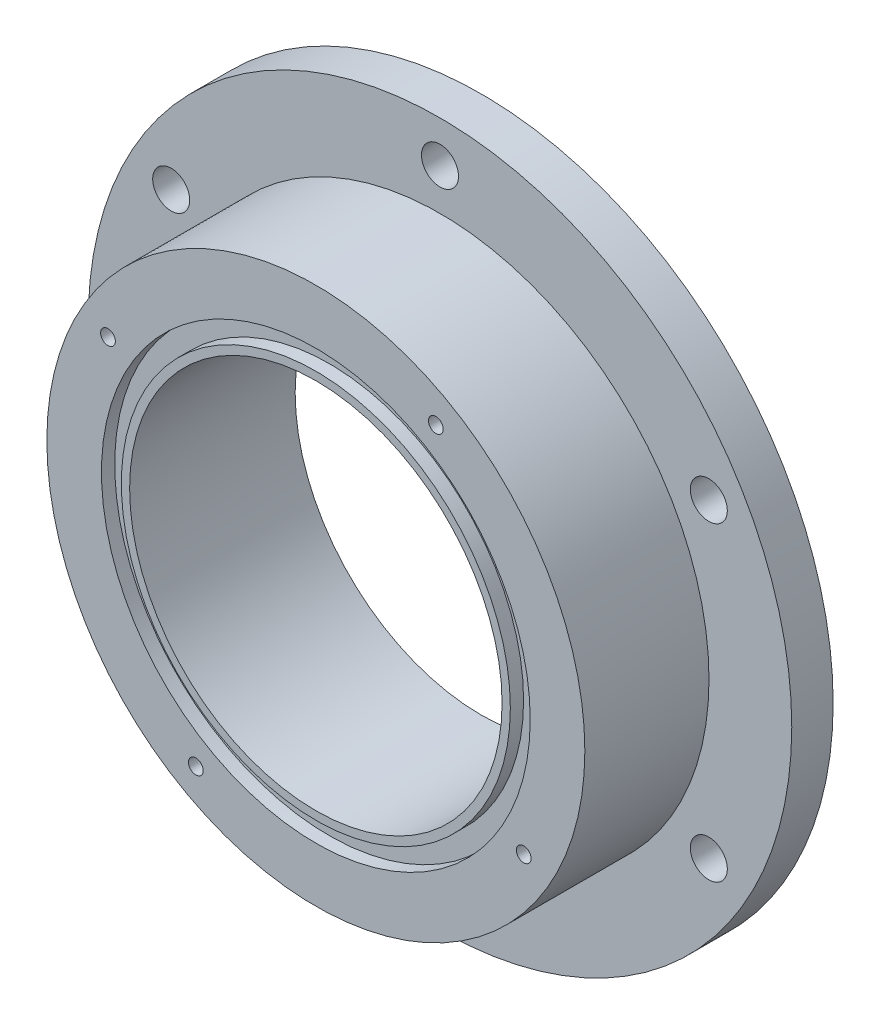
SolidWorks part; units mm, degrees
ref_plane "Front Plane" through (0, 0, 0) normal (0, 0, 1) x (1, 0, 0)
ref_plane "Top Plane" through (0, 0, 0) normal (0, 1, 0) x (1, 0, 0)
ref_plane "Right Plane" through (0, 0, 0) normal (1, 0, 0) x (0, 0, -1)
sketch "Sketch1" plane through (0, 0, 0) normal (0, 0, 1) x (1, 0, 0)
  circle A0 centre (0, 0) radius 53.975
  dimension "D1" = 107.95
extrude "Boss-Extrude1" add sketch "Sketch1" along normal blind 25.4
sketch "Sketch2" plane through (0, 0, 25.4) normal (0, 0, 1) x (1, 0, 0)
  circle A0 centre (0, 0) radius 41.275
  dimension "D1" = 82.55
extrude "Cut-Extrude1" cut sketch "Sketch2" along direction (0, 0, 1) on the side against the normal offset from surface (19.05 mm away) 6.35 flip side to cut
sketch "Sketch3" plane through (0, 0, 25.4) normal (0, 0, 1) x (1, 0, 0)
  circle A0 centre (0, 0) radius 28.575
  dimension "D1" = 57.15
extrude "Cut-Extrude2" cut sketch "Sketch3" against normal through all
sketch "Sketch6" plane through (0, 0, 25.4) normal (0, 0, 1) x (1, 0, 0)
  circle A0 centre (0, 0) radius 29.845
  circle A1 centre (0, 0) radius 32.893
  dimension "D1" = 59.69
  dimension "D2" = 3.048
extrude "Cut-Extrude3" cut sketch "Sketch6" against normal blind 2.032
hole_wizard "#4-40 Tapped Hole1" positions "Sketch7" profile "Sketch8" tap size "#4-40" standard "ANSI Inch"
sketch "Sketch7" plane through (0, 0, 25.4) normal (0, 0, 1) x (1, 0, 0)
  line L0 (0, 0) -> (0, 23.9657) construction
  line L2 (18.064, 9.5304) -> (18.2235, 9.5304) construction
  line L4 (0, 0) -> (38.7215, 67.0676) construction
  line L6 (67.9094, 49.8055) -> (68.0689, 49.8055) construction
  point P0 (18.415, 31.8957)
  dimension "D1" = 30
  dimension "D2" = 36.83
sketch "Sketch8" plane through (18.415, 31.8957, 25.4) normal (1, 0, 0) x (0, -1, 0)
  line L0 (0, 0) -> (0, 10.9662)
  line L1 (0, 10.9662) -> (1.1303, 10.287)
  line L2 (1.1303, 10.287) -> (1.1303, 0)
  line L5 (1.1303, 0) -> (0, 0)
  line L10 (0, 10.9662) -> (-1.1303, 10.287) construction
  line L11 (0, -6.35) -> (0, 107.95) construction
  dimension "Tap Drill Dia." = 2.2606
  dimension "Tap Drill Depth" = 10.287
  dimension "Drill Angle" = 118
pattern_circular "CirPattern2" count 4 over 360 about axis through (0, 0, 0) along (0, 0, 1) of "#4-40 Tapped Hole1"
sketch "Sketch9" plane through (0, 0, 0) normal (0, 0, -1) x (-1, 0, 0)
  circle A0 centre (0, 47.625) radius 2.8406
  dimension "D1" = 47.625
extrude "Cut-Extrude4" cut sketch "Sketch9" against normal through all
pattern_circular "CirPattern4" count 6 over 360 about axis through (0, 0, 0) along (0, 0, 1) of "Cut-Extrude4"
